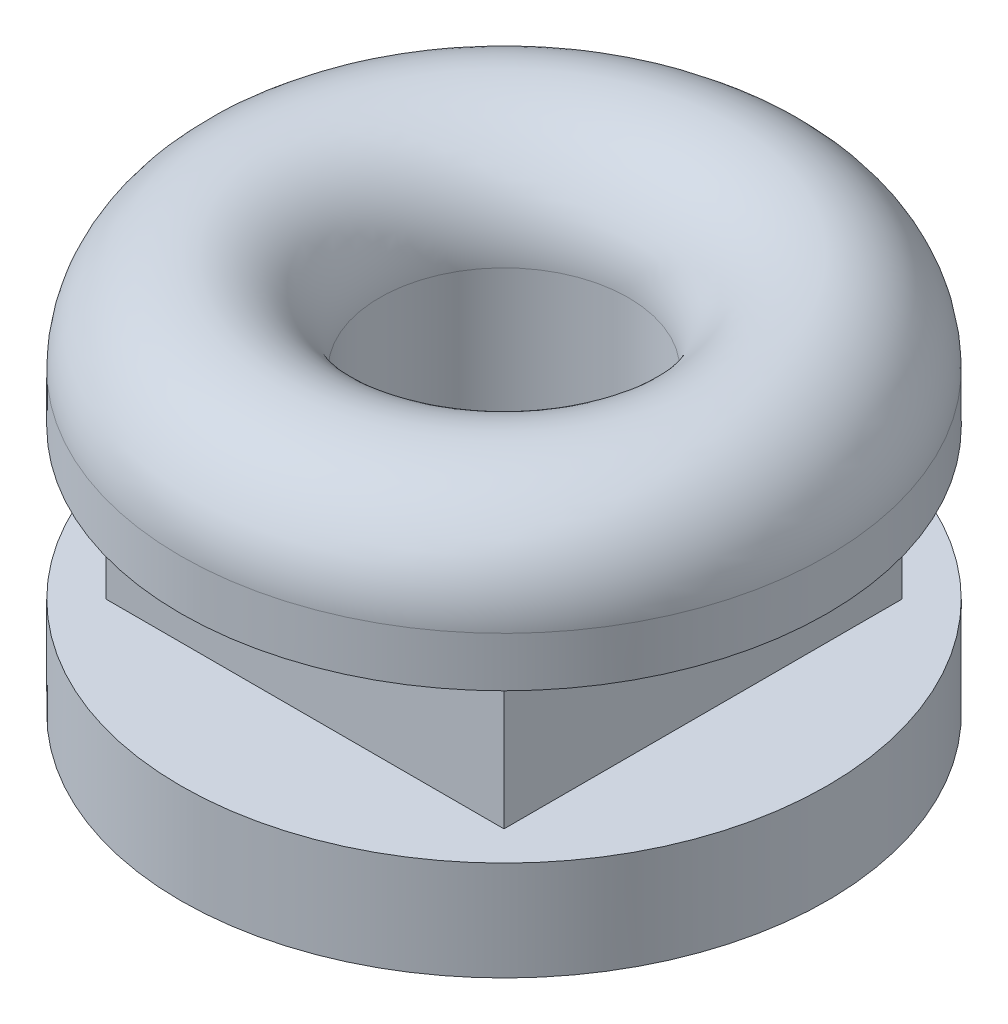
SolidWorks part; units mm, degrees
ref_plane "Спереди" through (0, 0, 0) normal (0, 0, 1) x (1, 0, 0)
ref_plane "Сверху" through (0, 0, 0) normal (0, 1, 0) x (1, 0, 0)
ref_plane "Справа" through (0, 0, 0) normal (1, 0, 0) x (0, 0, -1)
sketch "Sketch1" plane through (0, 0, 0) normal (0, 0, 1) x (1, 0, 0)
  line L0 (0, 0) -> (0, -8.7281) construction
  line L1 (-7.3364, 0) -> (3.3519, 0) construction
  line L3 (-2.5, -5) -> (-2.5, 1)
  line L8 (-2.5, -5) -> (-6.5, -5)
  line L9 (-6.5, -5) -> (-6.5, 1)
  arc A0 (-6.5, 1) -> (-2.5, 1) centre (-4.5, 1) cw
  dimension "D1" = 5
  dimension "D2" = 6
  dimension "D3" = 1
  dimension "D4" = 13
revolve "Revolve1" add sketch "Sketch1" angle 360 about L0
ref_plane "Plane2" through (0, -3, 0) normal (0, -1, 0) x (-1, 0, 0)
sketch "Sketch3" plane through (0, -3, 0) normal (0, -1, 0) x (-1, 0, 0)
  line L0 (0, 4.2945) -> (0, -3.6595) construction
  line L1 (-3.5563, 0) -> (4.0484, 0) construction
  line L3 (-4, 4) -> (4, 4)
  line L4 (-4, 4) -> (-4, -4)
  line L5 (-4, -4) -> (4, -4)
  line L6 (4, 4) -> (4, -4)
  circle A0 centre (0, 0) radius 6.5 construction
  circle A1 centre (0, 0) radius 6.5
  dimension "D1" = 8
extrude "Cut-Extrude1" cut sketch "Sketch3" against normal blind 3
ref_plane "Plane3" through (0, 0, 0) normal (0, -1, 0) x (-1, 0, 0)
sketch "Sketch4" plane through (0, 0, 0) normal (0, -1, 0) x (-1, 0, 0)
  line L0 (0, 6.81) -> (0, -7.516) construction
  line L1 (-8.42, 0) -> (10.0041, 0) construction
